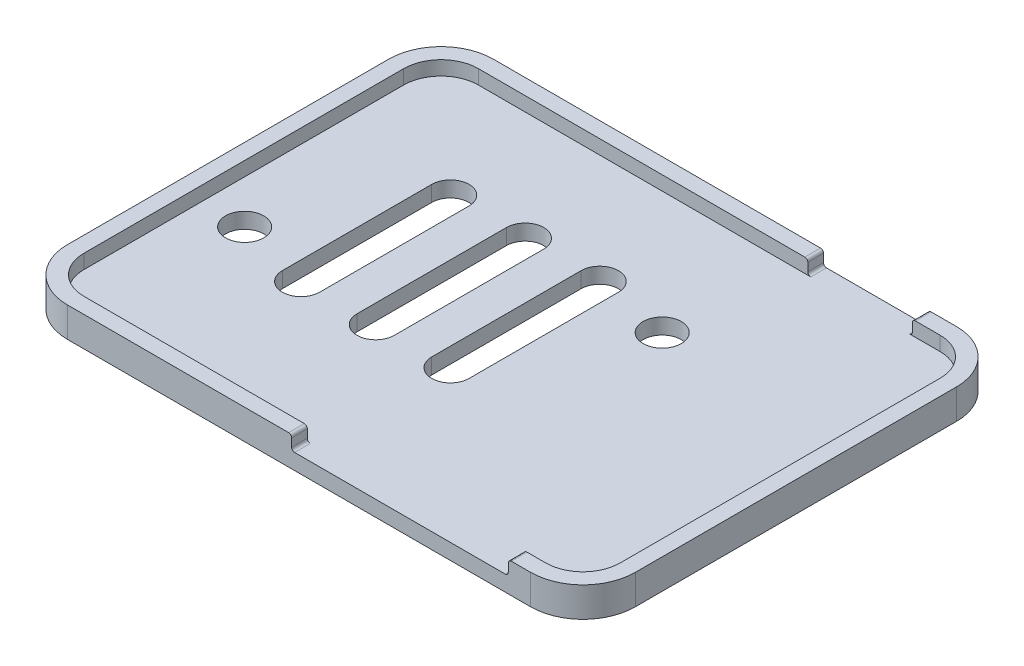
SolidWorks part; units mm, degrees
material "ABS PC"
ref_plane "Front Plane" through (0, 0, 0) normal (0, 0, 1) x (1, 0, 0)
ref_plane "Top Plane" through (0, 0, 0) normal (0, 1, 0) x (1, 0, 0)
ref_plane "Right Plane" through (0, 0, 0) normal (1, 0, 0) x (0, 0, -1)
sketch "Sketch1" plane through (0, 0, 0) normal (0, 1, 0) x (1, 0, 0)
  line L1 (-48.26, 36.195) -> (48.26, 36.195)
  line L2 (-48.26, 36.195) -> (-48.26, -36.195)
  line L3 (-48.26, -36.195) -> (48.26, -36.195)
  line L4 (48.26, 36.195) -> (48.26, -36.195)
  line L5 (-48.26, 36.195) -> (48.26, -36.195) construction
  line L6 (-48.26, -36.195) -> (48.26, 36.195) construction
  point P0 (0, 0)
  dimension "D1" = 96.52
  dimension "D2" = 72.39
extrude "Boss-Extrude1" add sketch "Sketch1" along normal blind 5.08
shell "Shell1" thickness 2.667
fillet "Fillet1" radius 6.35 4 edges at (-45.593, 3.8735, 33.528) (45.593, 3.8735, 33.528) (45.593, 3.8735, -33.528) (-45.593, 3.8735, -33.528)
fillet "Fillet2" radius 8.89 4 edges at (48.26, 2.54, 36.195) (48.26, 2.54, -36.195) (-48.26, 2.54, 36.195) (-48.26, 2.54, -36.195)
sketch "Sketch2" plane through (0, 0, 36.195) normal (0, 0, 1) x (1, 0, 0)
  line L0 (48.26, 5.08) -> (48.26, 0) construction
  line L1 (35.56, 2.667) -> (-1.27, 2.667)
  line L2 (35.56, 2.667) -> (35.56, 5.08)
  line L3 (35.56, 5.08) -> (-1.27, 5.08)
  line L4 (-1.27, 2.667) -> (-1.27, 5.08)
  line L5 (-39.243, 2.667) -> (39.243, 2.667) construction
  line L6 (-39.37, 5.08) -> (39.37, 5.08) construction
  dimension "D1" = 12.7
  dimension "D2" = 36.83
extrude "Cut-Extrude1" cut sketch "Sketch2" against normal blind 5.08 contours L3 L4 L1 L2
sketch "Sketch3" plane through (0, 0, -36.195) normal (0, 0, -1) x (-1, 0, 0)
  line L0 (-39.243, 2.667) -> (39.243, 2.667) construction
  line L1 (-34.544, 2.667) -> (-16.764, 2.667)
  line L2 (-34.544, 2.667) -> (-34.544, 5.08)
  line L3 (-34.544, 5.08) -> (-16.764, 5.08)
  line L4 (-16.764, 2.667) -> (-16.764, 5.08)
  line L5 (-39.37, 5.08) -> (39.37, 5.08) construction
  line L6 (-48.26, 0) -> (-48.26, 5.08) construction
  dimension "D1" = 17.78
  dimension "D2" = 13.716
extrude "Cut-Extrude2" cut sketch "Sketch3" against normal blind 5.08
fillet "Fillet3" radius 0.508 8 edges at (16.764, 5.08, -34.8615) (16.764, 2.667, -34.8615) (34.544, 5.08, -34.8615) (34.544, 2.667, -34.8615) (-1.27, 5.08, 34.8615) (-1.27, 2.667, 34.8615) (35.56, 5.08, 34.8615) (35.56, 2.667, 34.8615)
sketch "Sketch4" plane through (0, 0, 0) normal (0, -1, 0) x (1, 0, 0)
  circle A0 centre (-38.2316, 7.2232) radius 3.25
  circle A1 centre (12.8305, -12.7041) radius 3.25
extrude "Cut-Extrude3" cut sketch "Sketch4" against normal up to next
sketch "Sketch5" plane through (0, 0, 0) normal (0, -1, 0) x (1, 0, 0)
  line L0 (7.5623, -21.9675) -> (-32.9725, 17.5076) construction
  line L1 (-12.7051, 10.47) -> (-12.7051, -14.93) construction
  line L2 (-9.5301, 10.47) -> (-9.5301, -14.93)
  line L3 (-15.8801, 10.47) -> (-15.8801, -14.93)
  line L4 (-12.7051, -2.23) -> (-29.4209, -2.23) construction
  line L5 (-0.0051, 10.47) -> (-0.0051, -14.93) construction
  line L6 (3.1699, 10.47) -> (3.1699, -14.93)
  line L7 (-3.1801, 10.47) -> (-3.1801, -14.93)
  line L8 (-25.4051, 10.47) -> (-25.4051, -14.93) construction
  line L9 (-22.2301, 10.47) -> (-22.2301, -14.93)
  line L10 (-28.5801, 10.47) -> (-28.5801, -14.93)
  arc A0 (-9.5301, 10.47) -> (-15.8801, 10.47) centre (-12.7051, 10.47) ccw
  arc A1 (-15.8801, -14.93) -> (-9.5301, -14.93) centre (-12.7051, -14.93) ccw
  arc A2 (3.1699, 10.47) -> (-3.1801, 10.47) centre (-0.0051, 10.47) ccw
  arc A3 (-3.1801, -14.93) -> (3.1699, -14.93) centre (-0.0051, -14.93) ccw
  arc A4 (-22.2301, 10.47) -> (-28.5801, 10.47) centre (-25.4051, 10.47) ccw
  arc A5 (-28.5801, -14.93) -> (-22.2301, -14.93) centre (-25.4051, -14.93) ccw
  point P5 (-12.7051, -2.23)
  point P18 (-0.0051, -2.23)
  point P25 (-25.4051, -2.23)
  dimension "D1" = 3.175
  dimension "D2" = 25.4
  dimension "D3" = 2
  dimension "D4" = 2
extrude "Cut-Extrude4" cut sketch "Sketch5" against normal through all
